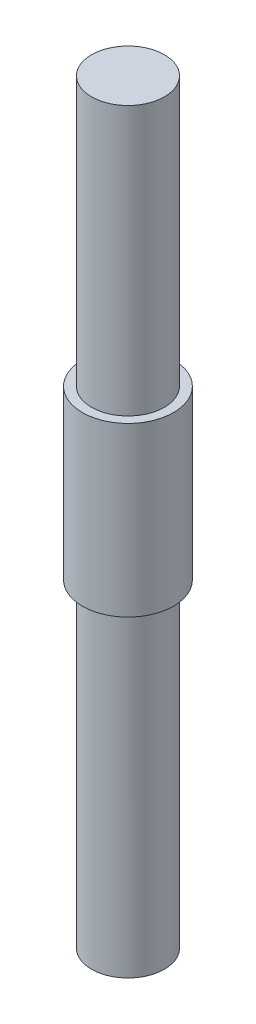
SolidWorks part; units mm, degrees
ref_plane "Front Plane" through (0, 0, 0) normal (0, 0, 1) x (1, 0, 0)
ref_plane "Top Plane" through (0, 0, 0) normal (0, 1, 0) x (1, 0, 0)
ref_plane "Right Plane" through (0, 0, 0) normal (1, 0, 0) x (0, 0, -1)
sketch "Sketch1" plane through (0, 0, 0) normal (0, 1, 0) x (1, 0, 0)
  circle A0 centre (0, 0) radius 5
  dimension "D1" = 10
extrude "Boss-Extrude1" add sketch "Sketch1" along normal blind 18.4
sketch "Sketch2" plane through (0, 18.4, 0) normal (0, 1, 0) x (1, 0, 0)
  circle A0 centre (0, 0) radius 4
  dimension "D1" = 8
extrude "Boss-Extrude2" add sketch "Sketch2" along normal blind 29.5
sketch "Sketch3" plane through (0, 0, 0) normal (0, -1, 0) x (1, 0, 0)
  circle A0 centre (0, 0) radius 4
  dimension "D1" = 8
extrude "Boss-Extrude3" add sketch "Sketch3" along normal blind 35
